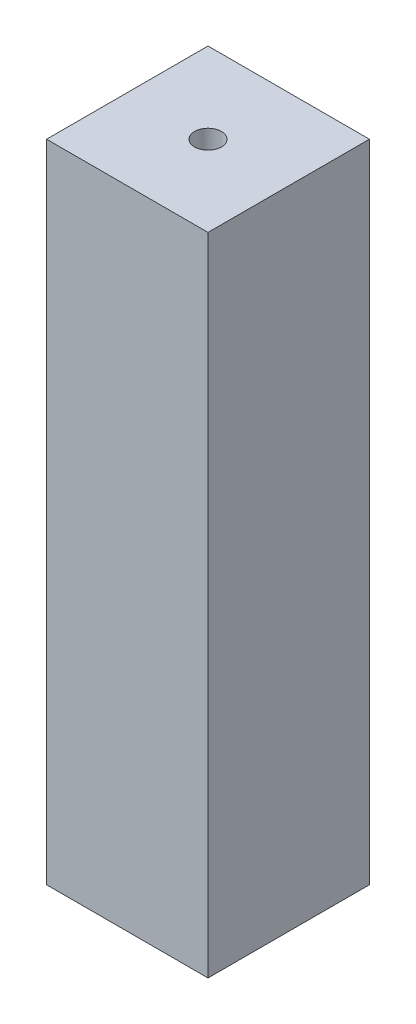
SolidWorks part; units mm, degrees
ref_plane "Front Plane" through (0, 0, 0) normal (0, 0, 1) x (1, 0, 0)
ref_plane "Top Plane" through (0, 0, 0) normal (0, 1, 0) x (1, 0, 0)
ref_plane "Right Plane" through (0, 0, 0) normal (1, 0, 0) x (0, 0, -1)
sketch "Sketch1" plane through (0, 0, 0) normal (0, 1, 0) x (1, 0, 0)
  line L1 (0, 0) -> (15, 0)
  line L2 (0, 0) -> (0, 15)
  line L3 (0, 15) -> (15, 15)
  line L4 (15, 0) -> (15, 15)
  dimension "D1" = 15
  dimension "15" = 15
extrude "Boss-Extrude1" add sketch "Sketch1" along normal blind 60
sketch "Sketch2" plane through (0, 60, 0) normal (0, 1, 0) x (1, 0, 0)
  line L0 (0, 15) -> (15, 0) construction
  circle A0 centre (7.5, 7.5) radius 1.25
  dimension "D1" = 2.5
extrude "Cut-Extrude1" cut sketch "Sketch2" against normal through all
